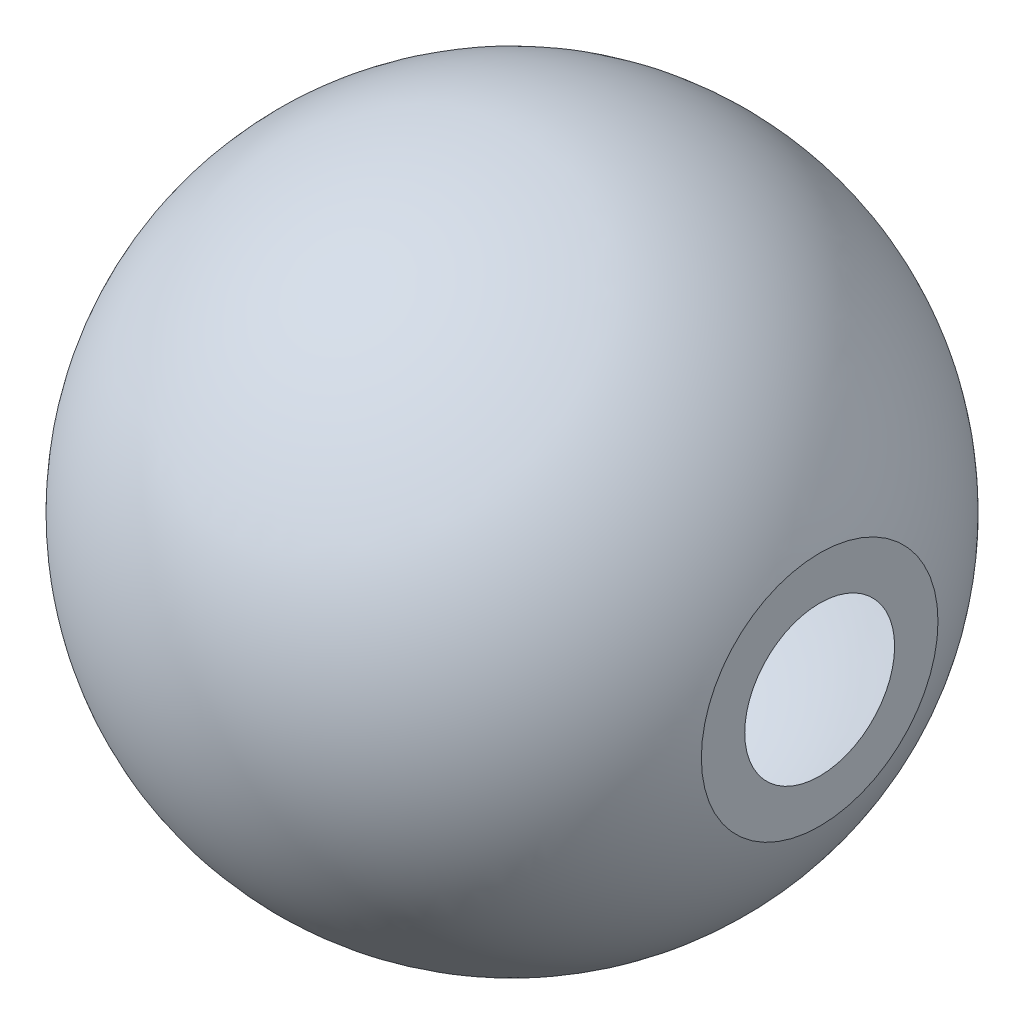
SolidWorks part; units mm, degrees
ref_plane "Front Plane" through (0, 0, 0) normal (0, 0, 1) x (1, 0, 0)
ref_plane "Top Plane" through (0, 0, 0) normal (0, 1, 0) x (1, 0, 0)
ref_plane "Right Plane" through (0, 0, 0) normal (1, 0, 0) x (0, 0, -1)
sketch "Sketch2" plane through (0, 0, 0) normal (0, 0, 1) x (1, 0, 0)
  line L1 (-76.2, 0) -> (-73.2, 0)
  line L3 (71.12, 17.3259) -> (71.12, 27.3567)
  line L4 (0, 0) -> (0, 96.2504) construction
  arc A3 (71.12, 17.3259) -> (-73.2, 0) centre (0, 0) ccw
  spline S0 degree 4 poles (-76.2, 0) (-76.1997, 3.3499) (-75.8605, 9.1425) (-74.5492, 17.2684) (-71.3778, 27.3961) (-67.3503, 36.1749) (-62.292, 44.3214) (-56.2535, 51.7709) (-49.3299, 58.4059) (-41.6302, 64.1219) (-33.2754, 68.829) (-24.3971, 72.4532) (-15.1349, 74.9374) (-5.6389, 76.242) (3.9415, 76.3482) (13.4556, 75.2562) (22.7546, 72.9848) (31.6968, 69.5691) (40.1421, 65.0628) (47.958, 59.5363) (55.022, 53.0767) (61.2234, 45.7846) (66.4649, 37.7755) (70.6909, 29.1183) (74.2549, 18.6426) (75.7815, 10.0778) (76.1997, 3.8259) (76.2, 0) knots 0 0 0 0 0 0.055863 0.096966 0.136917 0.176869 0.216822 0.256775 0.296729 0.336682 0.376635 0.416588 0.456542 0.496495 0.536377 0.576259 0.616141 0.656023 0.695905 0.735787 0.775669 0.815551 0.855432 0.895313 0.936199 1 1 1 1 1 construction
  spline S1 degree 4 poles (-76.2, 0) (-76.1997, 3.3499) (-75.8605, 9.1425) (-74.5492, 17.2684) (-71.3778, 27.3961) (-67.3503, 36.1749) (-62.292, 44.3214) (-56.2535, 51.7709) (-49.3299, 58.4059) (-41.6302, 64.1219) (-33.2754, 68.829) (-24.3971, 72.4532) (-15.1349, 74.9374) (-5.6389, 76.242) (3.9415, 76.3482) (13.4556, 75.2562) (22.7546, 72.9848) (31.6968, 69.5691) (40.1421, 65.0628) (47.958, 59.5363) (55.022, 53.0767) (61.2234, 45.7846) (66.0641, 38.3879) (68.9642, 32.6343) (70.5252, 28.9028) (71.12, 27.3567) knots 0 0 0 0 0 0.055863 0.096966 0.136917 0.176869 0.216822 0.256775 0.296729 0.336682 0.376635 0.416588 0.456542 0.496495 0.536377 0.576259 0.616141 0.656023 0.695905 0.735787 0.775669 0.815551 0.855432 0.883114 0.883114 0.883114 0.883114 0.883114
  dimension "D1" = 146.4
  dimension "D2" = 71.12
revolve "Revolve1" add sketch "Sketch2" angle 360 about L1
